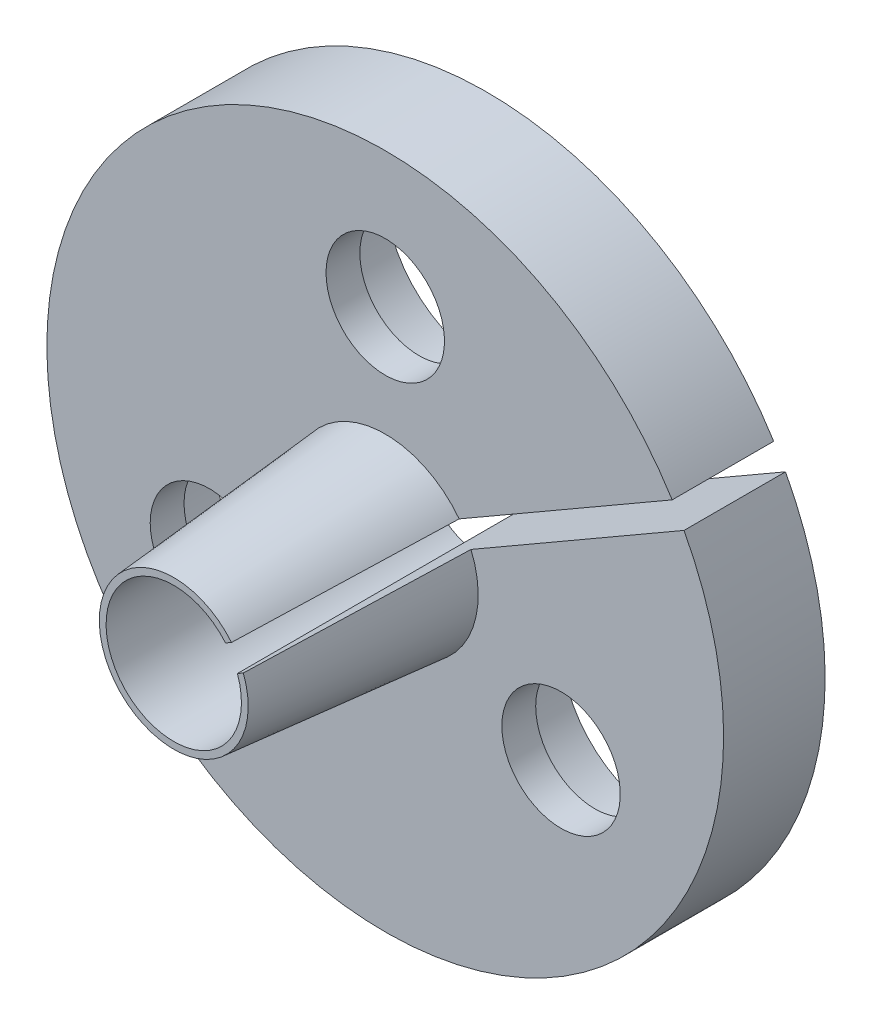
SolidWorks part; units mm, degrees
material "AISI 304"
ref_plane "Front Plane" through (0, 0, 0) normal (0, 0, 1) x (1, 0, 0)
ref_plane "Top Plane" through (0, 0, 0) normal (0, 1, 0) x (1, 0, 0)
ref_plane "Right Plane" through (0, 0, 0) normal (1, 0, 0) x (0, 0, -1)
sketch "Sketch3" plane through (0, 0, 0) normal (1, 0, 0) x (0, 0, -1)
  line L0 (0, 0) -> (-6.25, 0) construction
  line L1 (-6.25, 0) -> (-6.25, 2) construction
  line L2 (0, 2) -> (0, 2.7468)
  line L3 (-6.25, 2) -> (0, 2)
  line L4 (-6.25, 2.2) -> (0, 2.7468)
  line L5 (-6.25, 2.2) -> (-6.25, 2)
  line L6 (0, 0) -> (0, 2) construction
  dimension "D1" = 6.25
  dimension "D2" = 5
  dimension "D3" = 0.2
  dimension "D4" = 2
revolve "Revolve1" add sketch "Sketch3" angle 360 about L0
sketch "Sketch4" plane through (0, 0, 0) normal (0, 0, -1) x (-1, 0, 0)
  circle A0 centre (0, 0) radius 10
  circle A3 centre (0, 0) radius 2 construction
  circle A4 centre (0, 0) radius 2
  dimension "D1" = 20
extrude "Boss-Extrude4" add sketch "Sketch4" along normal blind 3
sketch "Sketch5" plane through (0, 0, -3) normal (0, 0, -1) x (-1, 0, 0)
  line L0 (0, 0) -> (0, 2) construction
  line L1 (0, 2) -> (0, 4.25) construction
  line L2 (0, 4.25) -> (0, 6) construction
  line L3 (0, 6) -> (0, 7.75) construction
  line L4 (0, 7.75) -> (0, 10) construction
  line L5 (-5.1962, -3) -> (-3.6806, -2.125) construction
  line L6 (-3.6806, -2.125) -> (-1.7321, -1) construction
  line L7 (-1.7321, -1) -> (0, 0) construction
  line L8 (-5.1962, -3) -> (-6.7117, -3.875) construction
  line L9 (-6.7117, -3.875) -> (-8.6603, -5) construction
  line L10 (3.6806, -2.125) -> (1.7321, -1) construction
  line L11 (3.6806, -2.125) -> (5.1962, -3) construction
  line L12 (5.1962, -3) -> (6.7117, -3.875) construction
  line L13 (6.7117, -3.875) -> (8.6603, -5) construction
  line L14 (1.7321, -1) -> (0, 0) construction
  circle A0 centre (0, 6) radius 1.75
  circle A1 centre (-5.1962, -3) radius 1.75
  circle A2 centre (5.1962, -3) radius 1.75
  circle A3 centre (0, 0) radius 2 construction
  circle A4 centre (0, 0) radius 10 construction
  dimension "D1" = 3.5
  dimension "D2" = 120
  dimension "D3" = 120
extrude "Cut-Extrude1" cut sketch "Sketch5" against normal through all
sketch "Sketch7" plane through (0, 0, -3) normal (0, 0, -1) x (-1, 0, 0)
  circle A0 centre (-5.1962, -3) radius 1.75 construction
  circle A1 centre (5.1962, -3) radius 1.75 construction
  circle A2 centre (0, 6) radius 1.75 construction
  circle A3 centre (-5.1962, -3) radius 1.75 construction
  circle A4 centre (5.1962, -3) radius 1.75 construction
  circle A5 centre (0, 6) radius 1.75 construction
  circle A6 centre (0, 6) radius 3
  circle A7 centre (5.1962, -3) radius 3
  circle A8 centre (-5.1962, -3) radius 3
  dimension "D1" = 6
extrude "Cut-Extrude3" cut sketch "Sketch7" against normal blind 2
sketch "Sketch6" plane through (0, 0, -3) normal (0, 0, -1) x (-1, 0, 0)
  line L0 (0, 0) -> (-8.6603, 5) construction
  line L1 (-2.5981, 1.5) -> (-5.1962, -3) construction
  line L2 (-2.5981, 1.5) -> (0, 6) construction
  line L3 (-8.8299, 4.6938) -> (-0.175, -0.3031)
  line L4 (-0.175, -0.3031) -> (0, 0)
  line L5 (0, 0) -> (0.175, 0.3031)
  line L6 (0.175, 0.3031) -> (-8.4799, 5.3)
  circle A0 centre (0, 0) radius 10 construction
  circle A1 centre (-5.1962, -3) radius 1.75 construction
  circle A2 centre (0, 6) radius 1.75 construction
  circle A3 centre (-5.1962, -3) radius 1.75 construction
  circle A4 centre (0, 6) radius 1.75 construction
  arc A5 (-8.4799, 5.3) -> (-8.8299, 4.6938) centre (0, 0) ccw
  dimension "D1" = 0.7
extrude "Cut-Extrude2" cut sketch "Sketch6" against normal through all
sketch "HolePositions" plane through (0, 0, -3) normal (0, 0, -1) x (-1, 0, 0)
  circle A0 centre (0, 0) radius 6 construction
  circle A1 centre (0, 6) radius 1.75 construction
  circle A2 centre (-5.1962, -3) radius 1.75 construction
  circle A3 centre (5.1962, -3) radius 1.75 construction
  circle A4 centre (0, 6) radius 1.75 construction
  circle A5 centre (-5.1962, -3) radius 1.75 construction
  circle A6 centre (5.1962, -3) radius 1.75 construction
  arc A7 (-8.8299, 4.6938) -> (-8.4799, 5.3) centre (0, 0) ccw construction
  arc A8 (-8.8299, 4.6938) -> (-8.4799, 5.3) centre (0, 0) ccw construction
  dimension "D1" = 12
  dimension "D2" = 10
